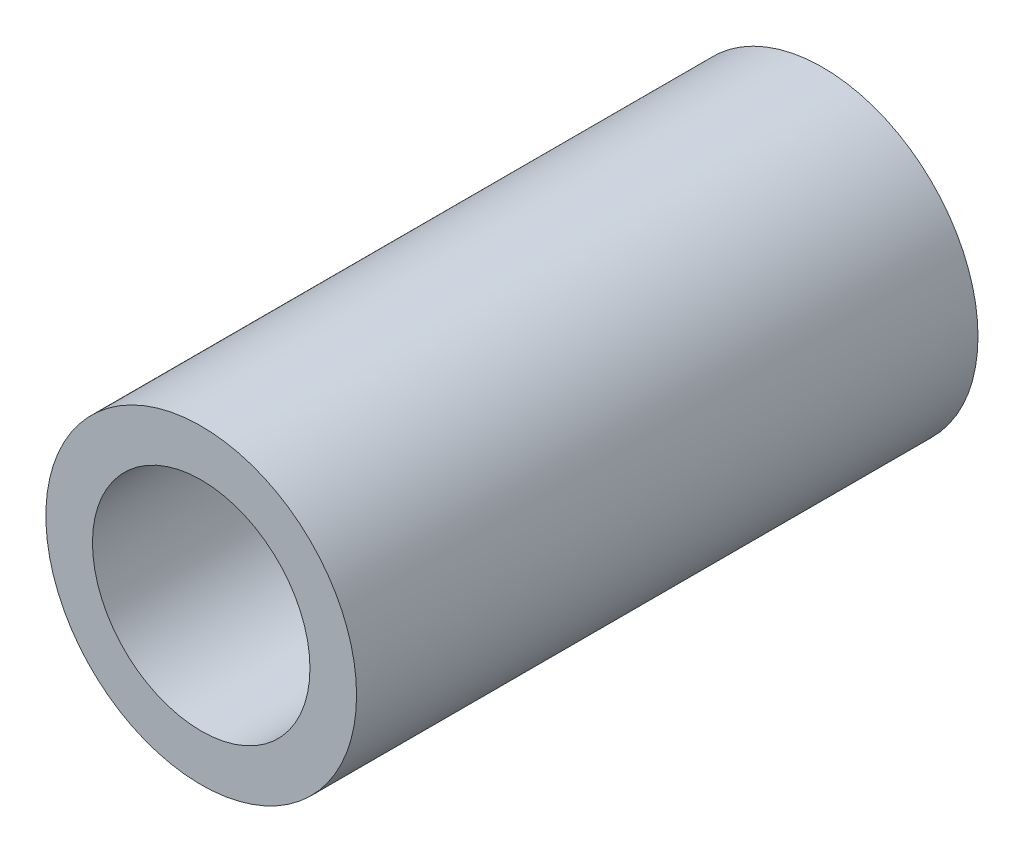
SolidWorks part; units mm, degrees
ref_plane "Front Plane" through (0, 0, 0) normal (0, 0, 1) x (1, 0, 0)
ref_plane "Top Plane" through (0, 0, 0) normal (0, 1, 0) x (1, 0, 0)
ref_plane "Right Plane" through (0, 0, 0) normal (1, 0, 0) x (0, 0, -1)
sketch "Sketch1" plane through (0, 0, 0) normal (0, 0, 1) x (1, 0, 0)
  circle A0 centre (0, 0) radius 2.5
  dimension "D1" = 5
extrude "Boss-Extrude1" add sketch "Sketch1" along normal blind 10
sketch "Sketch2" plane through (0, 0, 10) normal (0, 0, 1) x (1, 0, 0)
  circle A0 centre (0, 0) radius 1.75
  dimension "D1" = 3.5
extrude "Cut-Extrude1" cut sketch "Sketch2" against normal blind 10
